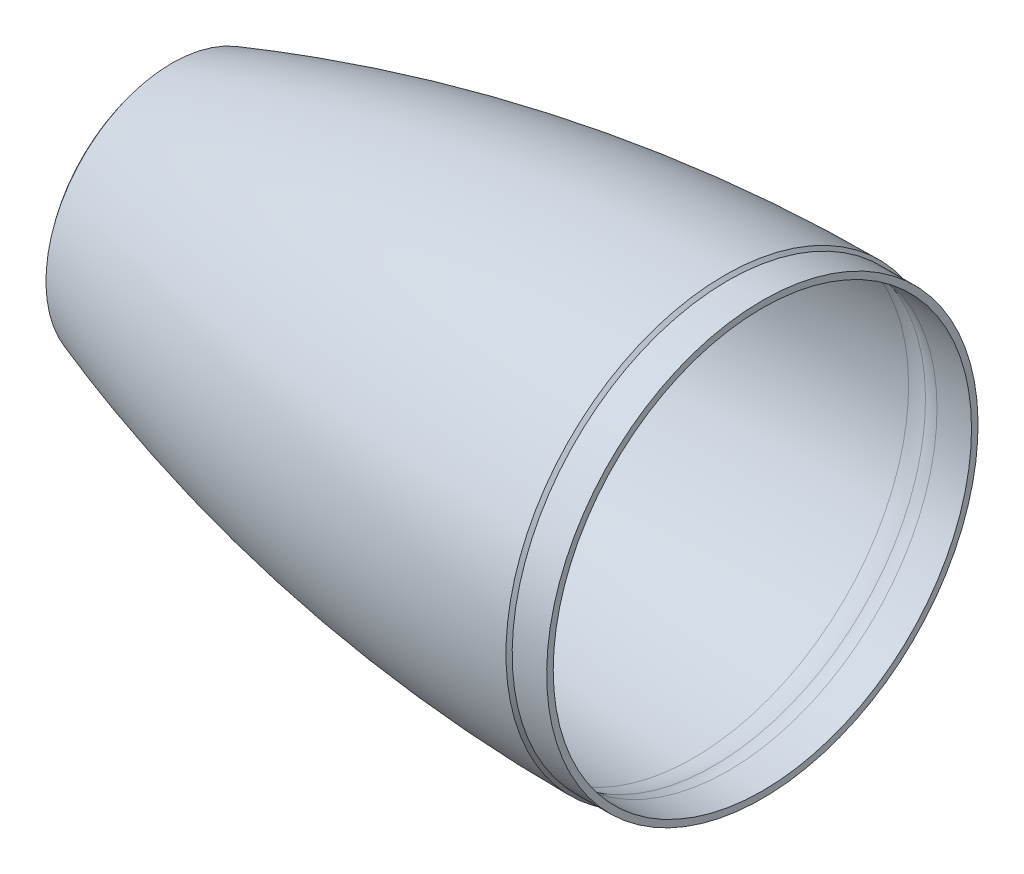
SolidWorks part; units mm, degrees
ref_plane "Front Plane" through (0, 0, 0) normal (0, 0, 1) x (1, 0, 0)
ref_plane "Top Plane" through (0, 0, 0) normal (0, 1, 0) x (1, 0, 0)
ref_plane "Right Plane" through (0, 0, 0) normal (1, 0, 0) x (0, 0, -1)
sketch "Sketch1" plane through (0, 0, 0) normal (0, 0, 1) x (1, 0, 0)
  line L4 (0, 0) -> (-304.8, 0) construction
  line L9 (0, 76.975) -> (0, 0) construction
  line L10 (0, 80.518) -> (50.8, 80.518) construction
  line L15 (1.143, 79.375) -> (13.843, 79.375)
  line L16 (0, 80.518) -> (1.143, 79.375)
  line L17 (1.143, 76.975) -> (13.843, 76.975)
  line L18 (13.843, 76.975) -> (13.843, 79.375)
  line L19 (-203.454, 46.355) -> (-203.454, 44.1325)
  line L20 (-203.454, 44.1325) -> (-199.644, 44.1325)
  line L21 (-199.644, 44.1325) -> (-195.834, 47.6691)
  arc A4 (0, 80.518) -> (-203.454, 46.355) centre (0, -542.3875) ccw
  arc A5 (-11.557, 79.2106) -> (-195.834, 47.6691) centre (0, -542.3875) ccw
  arc A6 (0, 79.318) -> (-203.0621, 45.2208) centre (0, -542.3875) ccw construction
  arc A10 (-4.0446, 77.9176) -> (1.143, 76.975) centre (1.143, 91.7214) ccw
  arc A13 (-11.557, 79.2106) -> (-4.0446, 77.9176) centre (-11.18, 58.9308) cw
  point P8 (-57.2734, -19.8104)
  point P9 (0, 313.4439)
  point P10 (-150.9565, 274.6984)
  dimension "D7" = 3.81
  dimension "D17" = 5.1876
  dimension "D8" = 3.81
  dimension "D16" = 12.7
  dimension "D1" = 161.036
  dimension "D2" = 50.8
  dimension "D3" = 203.454
  dimension "D4" = 92.71
  dimension "D6" = 88.265
  dimension "D9" = 304.8
  dimension "D12" = 12.7
  dimension "D13" = 158.75
  dimension "D14" = 45
  dimension "D15" = 2.4
  dimension "D5" = 1.2
revolve "Revolve1" add sketch "Sketch1" angle 360 about L4
fillet "Fillet1" radius 3.175 2 edges at (-199.644, 44.1325, 0) (-195.834, 47.6691, 0)
sketch "Sketch2" plane through (-203.454, 0, 0) normal (-1, 0, 0) x (0, 0, 1)
  circle A0 centre (0, 0) radius 44.1325 construction
  circle A1 centre (0, 0) radius 44.1325
  circle A2 centre (0, 0) radius 44.7325
  dimension "D1" = 0.6
extrude "Boss-Extrude1" add sketch "Sketch2" along normal blind 1.27
